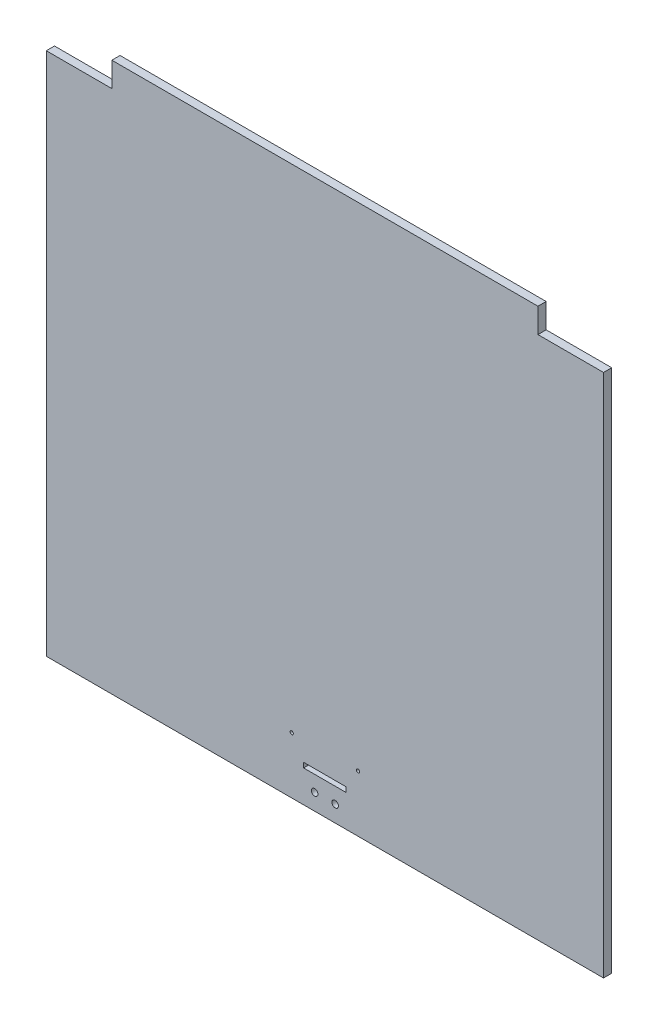
SolidWorks part; units mm, degrees
ref_plane "Plan de face" through (0, 0, 0) normal (0, 0, 1) x (1, 0, 0)
ref_plane "Plan de dessus" through (0, 0, 0) normal (0, 1, 0) x (1, 0, 0)
ref_plane "Plan de droite" through (0, 0, 0) normal (1, 0, 0) x (0, 0, -1)
sketch "Esquisse1" plane through (0, 0, 0) normal (0, 0, 1) x (1, 0, 0)
  line L1 (-340, 335) -> (340, 335)
  line L2 (-340, 335) -> (-340, -335)
  line L3 (-340, -335) -> (340, -335)
  line L4 (340, 335) -> (340, -335)
  dimension "D1" = 680
  dimension "D2" = 340
  dimension "D3" = 670
  dimension "D4" = 335
extrude "Boss.-Extru.1" add sketch "Esquisse1" along normal blind 10
sketch "Esquisse2" plane through (0, 0, 10) normal (0, 0, 1) x (1, 0, 0)
  line L0 (340, 335) -> (-340, 335) construction
  line L1 (-340, 335) -> (-260, 335)
  line L2 (-340, 335) -> (-340, 305)
  line L3 (-340, 305) -> (-260, 305)
  line L4 (-260, 335) -> (-260, 305)
  line L5 (340, 335) -> (260, 335)
  line L6 (340, 335) -> (340, 305)
  line L7 (340, 305) -> (260, 305)
  line L8 (260, 335) -> (260, 305)
  dimension "D1" = 30
  dimension "D2" = 30
  dimension "D3" = 80
  dimension "D4" = 80
extrude "Enlèv. mat.-Extru.1" cut sketch "Esquisse2" against normal through all
sketch "Esquisse3" plane through (0, 0, 10) normal (0, 0, 1) x (1, 0, 0)
  line L0 (340, -335) -> (340, 305) construction
  line L1 (-26, -290) -> (26, -290)
  line L2 (-26, -290) -> (-26, -296)
  line L3 (-26, -296) -> (26, -296)
  line L4 (26, -290) -> (26, -296)
  line L5 (-340, 305) -> (-340, -335) construction
  line L6 (-340, -335) -> (340, -335) construction
  dimension "D1" = 6
  dimension "D2" = 314
  dimension "D3" = 52
  dimension "D4" = 314
  dimension "D5" = 39
extrude "Enlèv. mat.-Extru.2" cut sketch "Esquisse3" against normal through all
sketch "Esquisse4" plane through (0, 0, 10) normal (0, 0, 1) x (1, 0, 0)
  line L0 (-340, -335) -> (340, -335) construction
  line L1 (-340, 305) -> (-340, -335) construction
  line L2 (340, -335) -> (340, 305) construction
  circle A0 centre (-12.5, -315) radius 4
  circle A1 centre (12.5, -315) radius 4
  dimension "D1" = 8
  dimension "D2" = 8
  dimension "D3" = 25
  dimension "D4" = 20
  dimension "D5" = 20
  dimension "D6" = 327.5
  dimension "D7" = 327.5
extrude "Enlèv. mat.-Extru.3" cut sketch "Esquisse4" against normal through all
sketch "Esquisse5" plane through (0, 0, 10) normal (0, 0, 1) x (1, 0, 0)
  line L0 (-340, -335) -> (340, -335) construction
  line L1 (-340, 305) -> (-340, -335) construction
  line L3 (340, -335) -> (340, 305) construction
  circle A0 centre (-40.5, -266) radius 2
  circle A1 centre (40.5, -266) radius 2
  dimension "D1" = 4
  dimension "D2" = 4
  dimension "D3" = 81
  dimension "D4" = 69
  dimension "D5" = 299.5
  dimension "D6" = 299.5
  dimension "D7" = 69
extrude "Enlèv. mat.-Extru.4" cut sketch "Esquisse5" against normal through all
